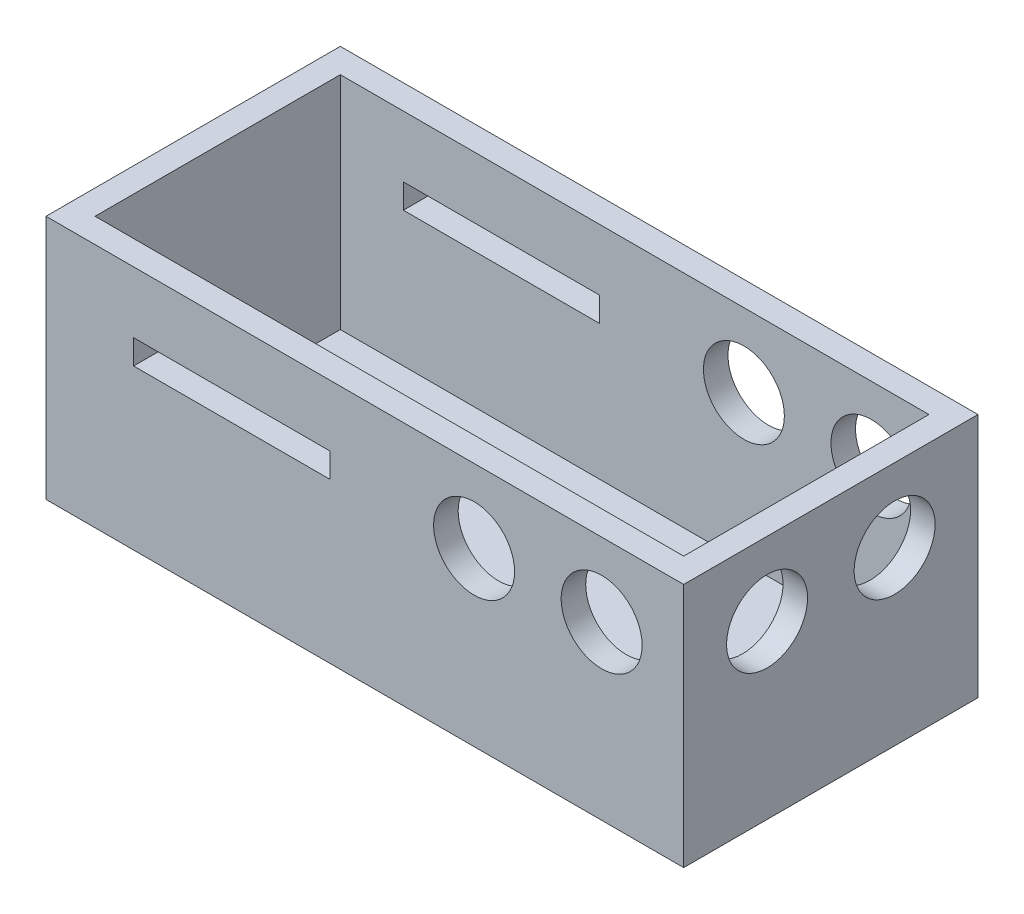
SolidWorks part; units mm, degrees
ref_plane "Front Plane" through (0, 0, 0) normal (0, 0, 1) x (1, 0, 0)
ref_plane "Top Plane" through (0, 0, 0) normal (0, 1, 0) x (1, 0, 0)
ref_plane "Right Plane" through (0, 0, 0) normal (1, 0, 0) x (0, 0, -1)
sketch "Sketch1" plane through (0, 0, 0) normal (0, 1, 0) x (1, 0, 0)
  line L1 (65, -30) -> (-65, -30)
  line L2 (65, -30) -> (65, 30)
  line L3 (65, 30) -> (-65, 30)
  line L4 (-65, -30) -> (-65, 30)
  line L5 (65, -30) -> (-65, 30) construction
  line L6 (65, 30) -> (-65, -30) construction
  line L11 (62.8333, -29) -> (-62.8333, 29) construction
  line L12 (62.8333, 29) -> (-62.8333, -29) construction
  point P1 (0, 0)
  point P6 (0, 0)
  dimension "D1" = 60
  dimension "D2" = 130
extrude "Boss-Extrude2" add sketch "Sketch1" along normal blind 50
shell "Shell1" thickness 5
sketch "Sketch2" plane through (65, 0, 0) normal (1, 0, 0) x (0, 0, -1)
  line L0 (0, 0) -> (0, 35)
  line L1 (0, 35) -> (4.75, 35)
  line L2 (0, 35) -> (-4.75, 35)
  circle A0 centre (13, 35) radius 8.25
  circle A1 centre (-13, 35) radius 8.25
  point P9 (0, 0)
  point P10 (0, 0)
  dimension "D4" = 16.5
  dimension "D5" = 16.5
  dimension "D1" = 35
extrude "Cut-Extrude1" cut sketch "Sketch2" against normal up to next contours L2 A1 | L2 A1 | L1 A0 | L1 A0
sketch "Sketch3" plane through (0, 0, 30) normal (0, 0, 1) x (1, 0, 0)
  line L0 (35.2742, 0) -> (35.2742, 35)
  line L1 (35.2742, 35) -> (40.0242, 35)
  line L2 (35.2742, 35) -> (30.5242, 35)
  circle A0 centre (48.2742, 35) radius 8.25
  circle A1 centre (22.2742, 35) radius 8.25
  point P3 (35.2742, 17.5)
  point P8 (0, 0)
extrude "Cut-Extrude2" cut sketch "Sketch3" against normal through all contours A1 | A0
sketch "Sketch4" plane through (0, 0, -30) normal (0, 0, -1) x (-1, 0, 0)
  line L0 (-48.2742, 35) -> (65, 35) construction
  line L1 (7.1407, 37.5) -> (47.1407, 37.5)
  line L2 (7.1407, 37.5) -> (7.1407, 32.5)
  line L3 (7.1407, 32.5) -> (47.1407, 32.5)
  line L4 (47.1407, 37.5) -> (47.1407, 32.5)
  line L5 (65, 50) -> (65, 0) construction
  point P9 (47.1407, 35)
  dimension "D1" = 5
  dimension "D2" = 40
extrude "Cut-Extrude3" cut sketch "Sketch4" against normal through all
